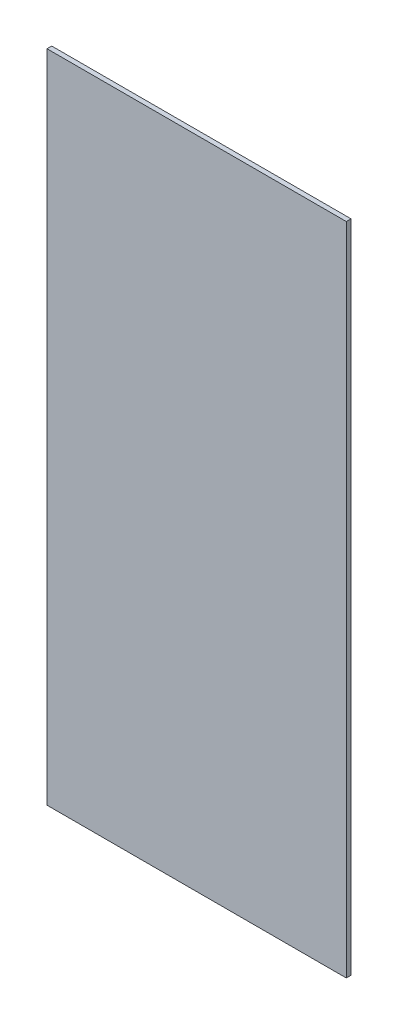
SolidWorks part; units mm, degrees
material "6061 Alloy"
ref_plane "Front Plane" through (0, 0, 0) normal (0, 0, 1) x (1, 0, 0)
ref_plane "Top Plane" through (0, 0, 0) normal (0, 1, 0) x (1, 0, 0)
ref_plane "Right Plane" through (0, 0, 0) normal (1, 0, 0) x (0, 0, -1)
sketch "Sketch2" plane through (0, 0, 0) normal (0, 0, 1) x (1, 0, 0)
  line L1 (-51.6256, 113) -> (51.6256, 113)
  line L2 (-51.6256, 113) -> (-51.6256, -113)
  line L3 (-51.6256, -113) -> (51.6256, -113)
  line L4 (51.6256, 113) -> (51.6256, -113)
  line L5 (-51.6256, 113) -> (51.6256, -113) construction
  line L6 (-51.6256, -113) -> (51.6256, 113) construction
  point P0 (0, 0)
  dimension "D1" = 226
  dimension "D2" = 103.2512
extrude "Boss-Extrude1" add sketch "Sketch2" along normal blind 1.6256
